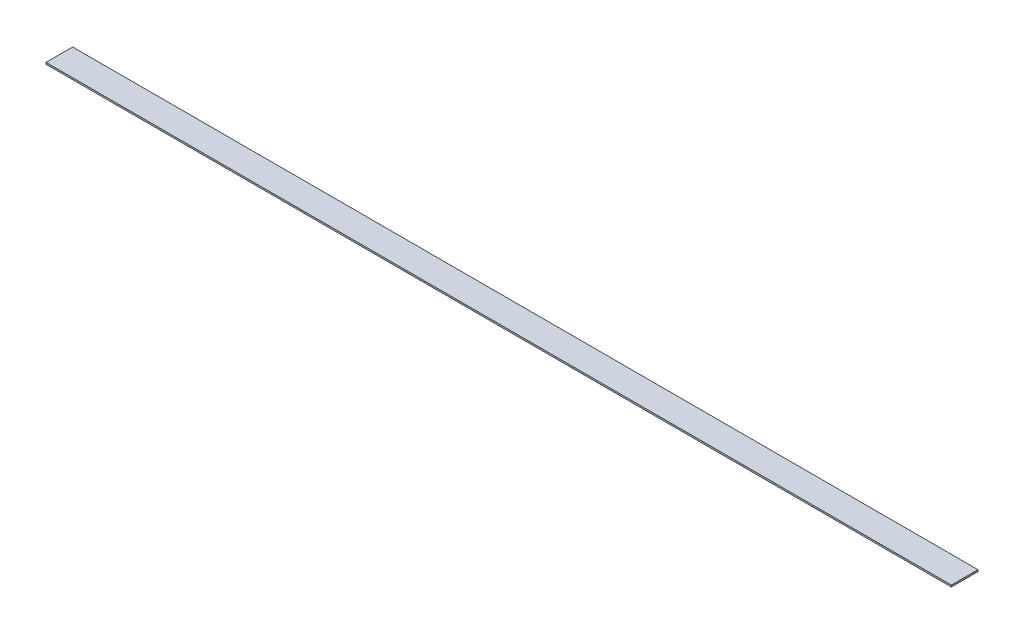
SolidWorks part; units mm, degrees
ref_plane "Front Plane" through (0, 0, 0) normal (0, 0, 1) x (1, 0, 0)
ref_plane "Top Plane" through (0, 0, 0) normal (0, 1, 0) x (1, 0, 0)
ref_plane "Right Plane" through (0, 0, 0) normal (1, 0, 0) x (0, 0, -1)
sketch "Sketch1" plane through (0, 0, 0) normal (0, 1, 0) x (1, 0, 0)
  line L1 (0, 0) -> (863.6, 0)
  line L2 (0, 0) -> (0, 25.4)
  line L3 (0, 25.4) -> (863.6, 25.4)
  line L4 (863.6, 0) -> (863.6, 25.4)
  dimension "D1" = 25.4
  dimension "D2" = 863.6
extrude "Boss-Extrude1" add sketch "Sketch1" along normal blind 1.5875
